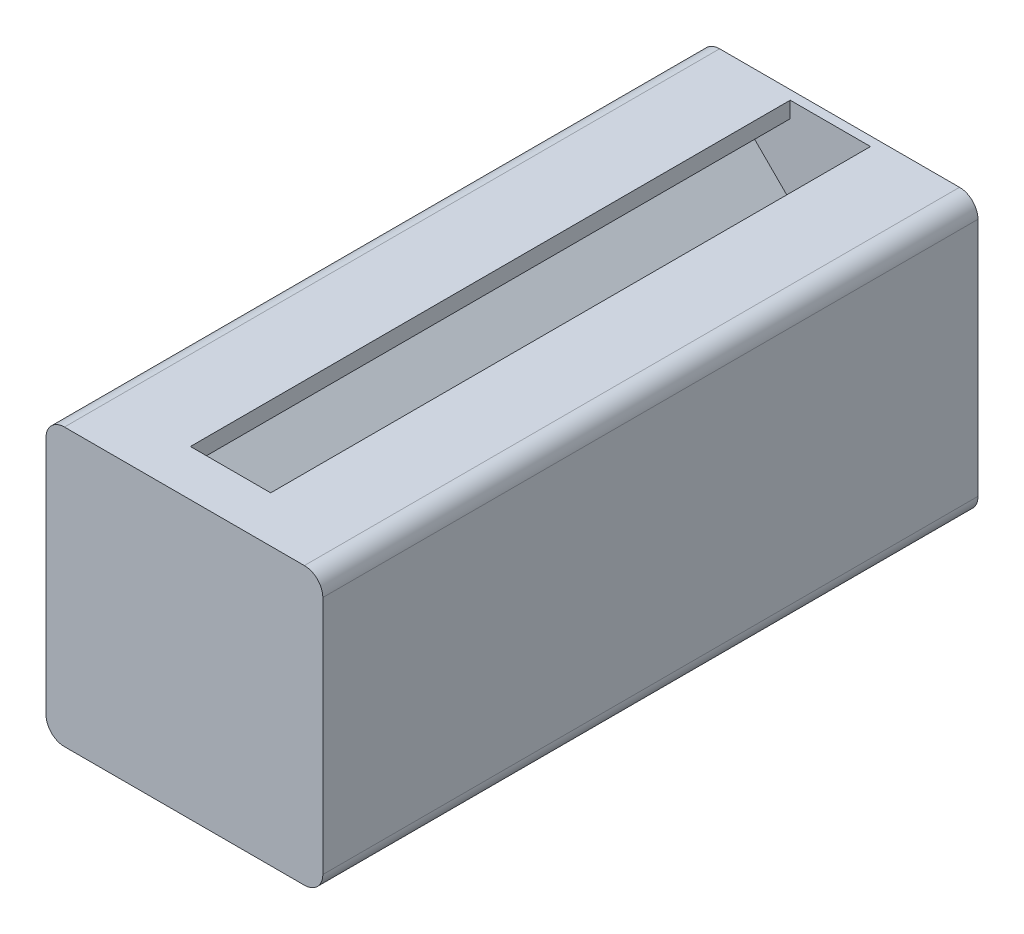
SolidWorks part; units mm, degrees
material "Lega 1060"
ref_plane "Front Plane" through (0, 0, 0) normal (0, 0, 1) x (1, 0, 0)
ref_plane "Top Plane" through (0, 0, 0) normal (0, 1, 0) x (1, 0, 0)
ref_plane "Right Plane" through (0, 0, 0) normal (1, 0, 0) x (0, 0, -1)
sketch "Sketch1" plane through (0, 0, 0) normal (0, 0, 1) x (1, 0, 0)
  line L0 (-8.46, 9.66) -> (-4.55, 5.75)
  line L1 (-15, -15) -> (-4.35, -15)
  line L2 (-15, -15) -> (-15, -4.35)
  line L3 (-15, 15) -> (-4.35, 15)
  line L4 (15, -15) -> (15, -4.35)
  line L5 (-15, -15) -> (15, 15) construction
  line L6 (-15, 15) -> (15, -15) construction
  line L7 (-4.5783, -5.75) -> (4.6181, -5.75)
  line L8 (-5.75, -4.55) -> (-5.75, 4.55)
  line L9 (-4.55, 5.75) -> (4.55, 5.75)
  line L10 (5.75, -4.55) -> (5.75, 4.55)
  line L11 (-5.75, -5.75) -> (5.75, 5.75) construction
  line L12 (-5.75, 5.75) -> (5.75, -5.75) construction
  line L13 (-8.46, 9.66) -> (-8.46, 13.26)
  line L14 (-8.46, 13.26) -> (-4.35, 13.26)
  line L15 (-4.35, 13.26) -> (-4.35, 15)
  line L16 (-9.66, 8.46) -> (-5.75, 4.55)
  line L17 (-9.66, 8.46) -> (-13.26, 8.46)
  line L18 (-13.26, 8.46) -> (-13.26, 4.35)
  line L19 (-13.26, 4.35) -> (-15, 4.35)
  line L20 (9.66, 8.46) -> (5.75, 4.55)
  line L21 (8.46, 9.66) -> (8.46, 13.26)
  line L22 (8.46, 13.26) -> (4.35, 13.26)
  line L23 (4.35, 13.26) -> (4.35, 15)
  line L24 (8.46, 9.66) -> (4.55, 5.75)
  line L25 (9.66, 8.46) -> (13.26, 8.46)
  line L26 (13.26, 8.46) -> (13.26, 4.35)
  line L27 (13.26, 4.35) -> (15, 4.35)
  line L28 (9.66, -8.46) -> (5.75, -4.55)
  line L29 (-9.66, -8.46) -> (-13.26, -8.46)
  line L30 (-13.26, -8.46) -> (-13.26, -4.35)
  line L31 (-13.26, -4.35) -> (-15, -4.35)
  line L32 (-9.66, -8.46) -> (-5.75, -4.55)
  line L33 (-8.4202, -9.5919) -> (-8.4202, -13.26)
  line L34 (-8.4202, -13.26) -> (-4.35, -13.26)
  line L35 (-4.35, -13.26) -> (-4.35, -15)
  line L36 (-8.4202, -9.5919) -> (-4.5783, -5.75)
  line L37 (9.66, -8.46) -> (13.26, -8.46)
  line L38 (13.26, -8.46) -> (13.26, -4.35)
  line L39 (13.26, -4.35) -> (15, -4.35)
  line L40 (8.46, -9.5919) -> (4.6181, -5.75)
  line L41 (8.46, -9.5919) -> (8.46, -13.26)
  line L42 (8.46, -13.26) -> (4.35, -13.26)
  line L43 (4.35, -13.26) -> (4.35, -15)
  line L44 (-15, 4.35) -> (-15, 15)
  line L45 (15, 4.35) -> (15, 15)
  line L46 (4.35, -15) -> (15, -15)
  line L47 (4.35, 15) -> (15, 15)
  circle A0 centre (0, 0) radius 3
  circle A1 centre (11.73, 11.73) radius 1.65
  circle A2 centre (11.73, -11.73) radius 1.65
  circle A3 centre (-11.73, -11.73) radius 1.65
  circle A4 centre (-11.73, 11.73) radius 1.65
  point P0 (0, 0)
  dimension "D3" = 6
  dimension "D10" = 3.3
  dimension "D1" = 30
  dimension "D2" = 30
  dimension "D4" = 11.5
  dimension "D5" = 11.5
  dimension "D6" = 10.65
  dimension "D7" = 4.11
  dimension "D8" = 1.74
  dimension "D9" = 3.6
  dimension "D11" = 3.27
  dimension "D12" = 3.27
  dimension "D13" = 3.27
  dimension "D14" = 3.27
  dimension "D15" = 3.27
  dimension "D16" = 3.27
  dimension "D17" = 3.27
  dimension "D18" = 3.27
extrude "Boss-Extrude1" add sketch "Sketch1" along normal blind 65
fillet "Fillet1" radius 2 4 edges at (-15, -15, 32.5) (15, -15, 32.5) (15, 15, 32.5) (-15, 15, 32.5)
sketch "Schizzo1" plane through (0, 0, 65) normal (0, 0, 1) x (1, 0, 0)
  line L0 (13, 15) -> (4.35, 15) construction
  line L1 (15, 4.35) -> (15, 13) construction
  line L2 (15, -13) -> (15, -4.35) construction
  line L3 (4.35, -15) -> (13, -15) construction
  line L4 (-13, -15) -> (-4.35, -15) construction
  line L5 (-15, -4.35) -> (-15, -13) construction
  line L6 (-4.35, 15) -> (-13, 15) construction
  line L7 (-15, 13) -> (-15, 4.35) construction
  line L8 (13, 15) -> (4.35, 15)
  line L9 (15, 4.35) -> (15, 13)
  line L10 (15, -13) -> (15, -4.35)
  line L11 (4.35, -15) -> (13, -15)
  line L12 (-13, -15) -> (-4.35, -15)
  line L13 (-15, -4.35) -> (-15, -13)
  line L14 (-4.35, 15) -> (-13, 15)
  line L15 (-15, 13) -> (-15, 4.35)
  line L16 (-4.35, 15) -> (4.35, 15)
  line L17 (15, 4.35) -> (15, -4.35)
  line L18 (4.35, -15) -> (-4.35, -15)
  line L19 (-15, -4.35) -> (-15, 4.35)
  arc A0 (15, 13) -> (13, 15) centre (13, 13) ccw construction
  arc A1 (13, -15) -> (15, -13) centre (13, -13) ccw construction
  arc A2 (-15, -13) -> (-13, -15) centre (-13, -13) ccw construction
  arc A3 (-13, 15) -> (-15, 13) centre (-13, 13) ccw construction
  arc A4 (15, 13) -> (13, 15) centre (13, 13) ccw
  arc A5 (13, -15) -> (15, -13) centre (13, -13) ccw
  arc A6 (-15, -13) -> (-13, -15) centre (-13, -13) ccw
  arc A7 (-13, 15) -> (-15, 13) centre (-13, 13) ccw
extrude "Estrusione-Estrusione1" add sketch "Schizzo1" along normal blind 5
sketch "Schizzo2" plane through (0, 0, 0) normal (0, 0, -1) x (-1, 0, 0)
  line L0 (-13, 15) -> (13, 15)
  line L1 (-15, 13) -> (-15, -13)
  line L2 (15, 13) -> (15, -13)
  line L3 (13, -15) -> (-13, -15)
  arc A0 (-15, -13) -> (-13, -15) centre (-13, -13) ccw construction
  arc A1 (13, -15) -> (15, -13) centre (13, -13) ccw construction
  arc A2 (15, 13) -> (13, 15) centre (13, 13) ccw construction
  arc A3 (-13, 15) -> (-15, 13) centre (-13, 13) ccw construction
  arc A4 (-15, -13) -> (-13, -15) centre (-13, -13) ccw
  arc A5 (13, -15) -> (15, -13) centre (13, -13) ccw
  arc A6 (15, 13) -> (13, 15) centre (13, 13) ccw
  arc A7 (-13, 15) -> (-15, 13) centre (-13, 13) ccw
extrude "Estrusione-Estrusione2" add sketch "Schizzo2" along normal blind 1
sketch "Schizzo3" plane through (15, 0, 0) normal (1, 0, 0) x (0, 0, -1)
  line L1 (-65, 4.35) -> (0, 4.35)
  line L2 (-65, 4.35) -> (-65, -4.35)
  line L3 (-65, -4.35) -> (0, -4.35)
  line L4 (0, 4.35) -> (0, -4.35)
extrude "Estrusione-Estrusione3" add sketch "Schizzo3" against normal blind 1
